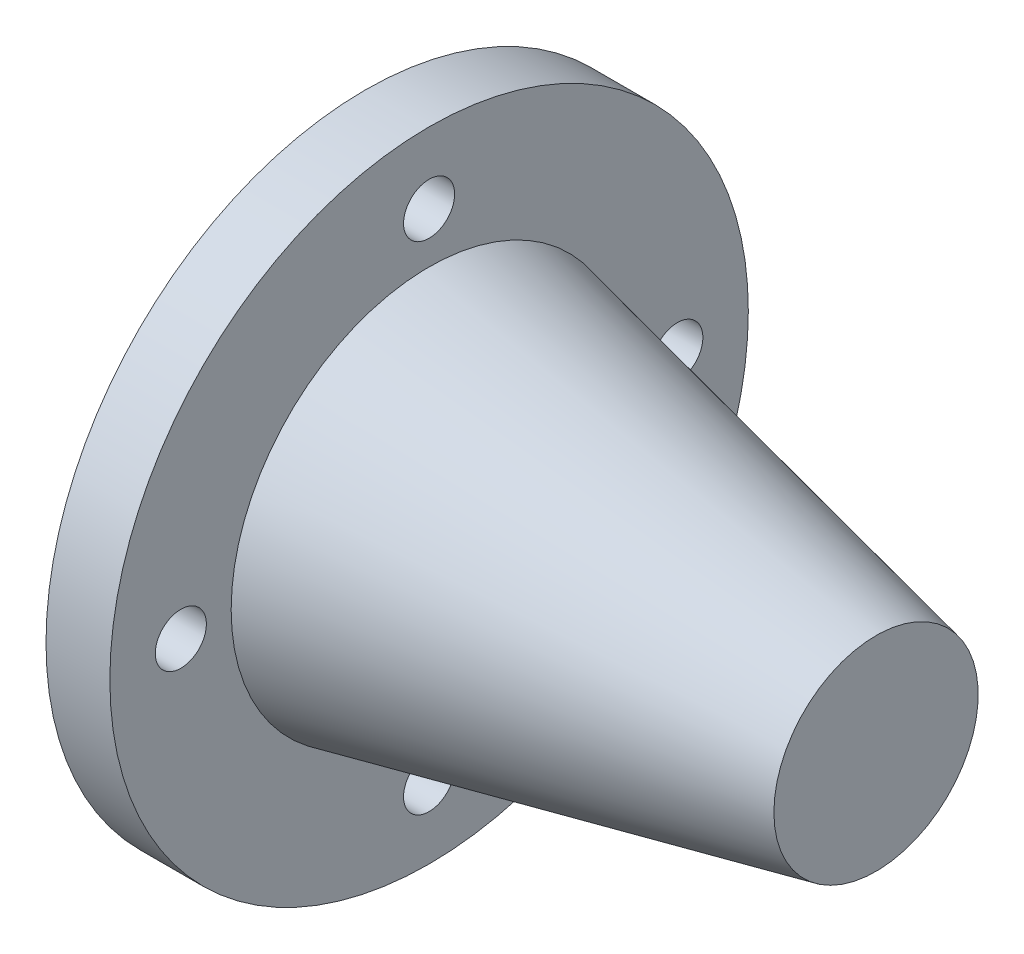
SolidWorks part; units mm, degrees
ref_plane "Ebene vorne" through (0, 0, 0) normal (0, 0, 1) x (1, 0, 0)
ref_plane "Ebene oben" through (0, 0, 0) normal (0, 1, 0) x (1, 0, 0)
ref_plane "Ebene rechts" through (0, 0, 0) normal (1, 0, 0) x (0, 0, -1)
sketch "Skizze1" plane through (0, 0, 0) normal (0, 0, 1) x (1, 0, 0)
  line L0 (0, 12.75) -> (3, 12.75)
  line L1 (3, 12.75) -> (3, 9.75)
  line L2 (3, 9.75) -> (23, 7.5)
  line L3 (0, 25) -> (0, 12.75)
  line L4 (38, 0) -> (40, 0)
  line L5 (40, 0) -> (40, 8)
  line L6 (40, 8) -> (5, 15.5)
  line L7 (5, 15.5) -> (5, 25)
  line L8 (-34.8425, 0) -> (59.0368, 0) construction
  line L9 (5, 25) -> (0, 25)
  line L13 (23, 7.5) -> (38, 0)
  dimension "D1" = 12.75
  dimension "D2" = 25
  dimension "D3" = 3
  dimension "D4" = 40
  dimension "D5" = 8
  dimension "D6" = 9.5
  dimension "D7" = 7.5
  dimension "D8" = 5
  dimension "D9" = 3
  dimension "D10" = 15
  dimension "D11" = 20
revolve "Rotation1" add sketch "Skizze1" angle 360 about L8
sketch "Skizze2" plane through (0, 0, 0) normal (-1, 0, 0) x (0, 0, 1)
  line L0 (0, 0) -> (-19.44, 0)
  circle A0 centre (0, 0) radius 19.44
  dimension "D1" = 38.88
hole_wizard "Ø4.0 (4) Durchmesser Bohrung1" positions "Skizze4" profile "Skizze5" hole size "Ø4.0" standard "ANSI Metrisch" end condition up to next
sketch "Skizze4" plane through (0, 0, 0) normal (-1, 0, 0) x (0, 0, 1)
  point P0 (-19.44, 0)
sketch "Skizze5" plane through (0, 0, -19.44) normal (0, 1, 0) x (0, 0, 1)
  line L0 (0, 0) -> (0, 5.001)
  line L1 (0, 5.001) -> (2, 5.001)
  line L2 (2, 5.001) -> (2, 0)
  line L5 (2, 0) -> (0, 0)
  line L11 (0, -6.35) -> (0, 107.95) construction
  dimension "Bohrerdurchmesser" = 4
  dimension "Bohrungstiefe" = 5.001
pattern_circular "Kreismuster1" count 4 over 360 about axis through (0, 0, 0) along (1, 0, 0) of "Ø4.0 (4) Durchmesser Bohrung1"
